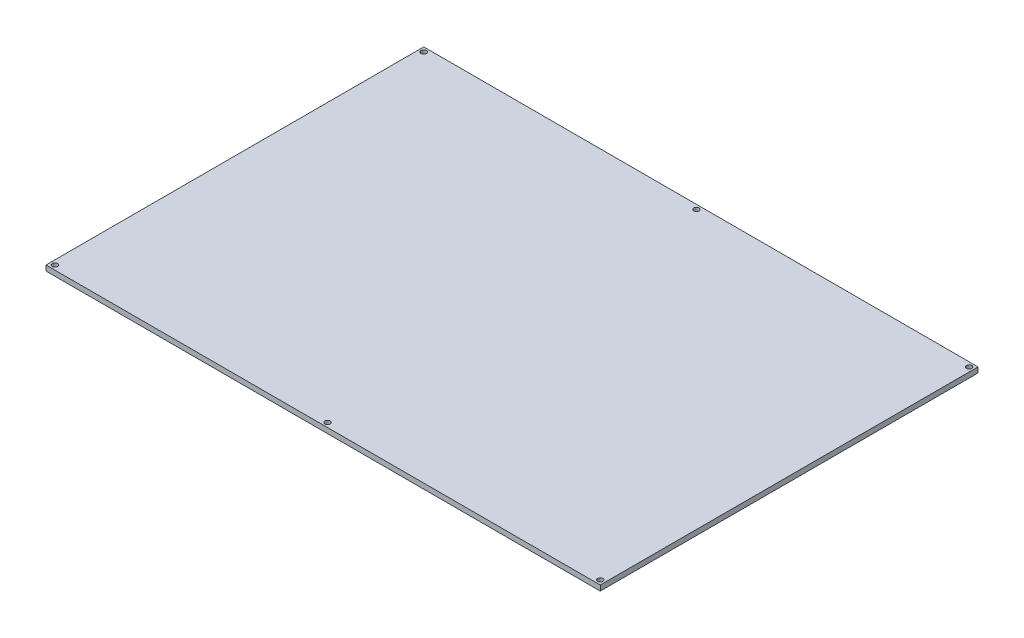
SolidWorks part; units mm, degrees
ref_plane "Front Plane" through (0, 0, 0) normal (0, 0, 1) x (1, 0, 0)
ref_plane "Top Plane" through (0, 0, 0) normal (0, 1, 0) x (1, 0, 0)
ref_plane "Right Plane" through (0, 0, 0) normal (1, 0, 0) x (0, 0, -1)
sketch "Sketch1" plane through (0, 0, 0) normal (0, 1, 0) x (1, 0, 0)
  line L1 (-314, 214) -> (0, 214)
  line L2 (-314, 214) -> (-314, 0)
  line L3 (-314, 0) -> (0, 0)
  line L4 (0, 214) -> (0, 0)
  circle A0 centre (-311.5, 211.5) radius 1.5
  circle A1 centre (-311.5, 2.5) radius 1.5
  circle A2 centre (-2.5, 2.5) radius 1.5
  circle A3 centre (-2.5, 211.5) radius 1.5
  dimension "D3" = 3
  dimension "D1" = 314
  dimension "D2" = 214
  dimension "D4" = 2.5
  dimension "D5" = 2.5
  dimension "D6" = 2.5
  dimension "D7" = 2.5
  dimension "D8" = 2.5
  dimension "D9" = 2.5
  dimension "D10" = 2.5
  dimension "D11" = 2.5
extrude "Boss-Extrude1" add sketch "Sketch1" along normal blind 3
sketch "Sketch2" plane through (0, 0, 0) normal (0, -1, 0) x (1, 0, 0)
  line L0 (-157, -2.5) -> (-157, -211.5) construction
  line L1 (-314, 0) -> (0, 0) construction
  line L2 (0, -214) -> (-314, -214) construction
  line L3 (-314, -214) -> (0, 0) construction
  circle A0 centre (-157, -2.5) radius 1.5
  circle A1 centre (-157, -211.5) radius 1.5
  circle A2 centre (-2.5, -2.5) radius 1.5 construction
  point P14 (-157, -107)
  dimension "D1" = 2.5
  dimension "D2" = 2.5
extrude "Cut-Extrude1" cut sketch "Sketch2" against normal blind 10
